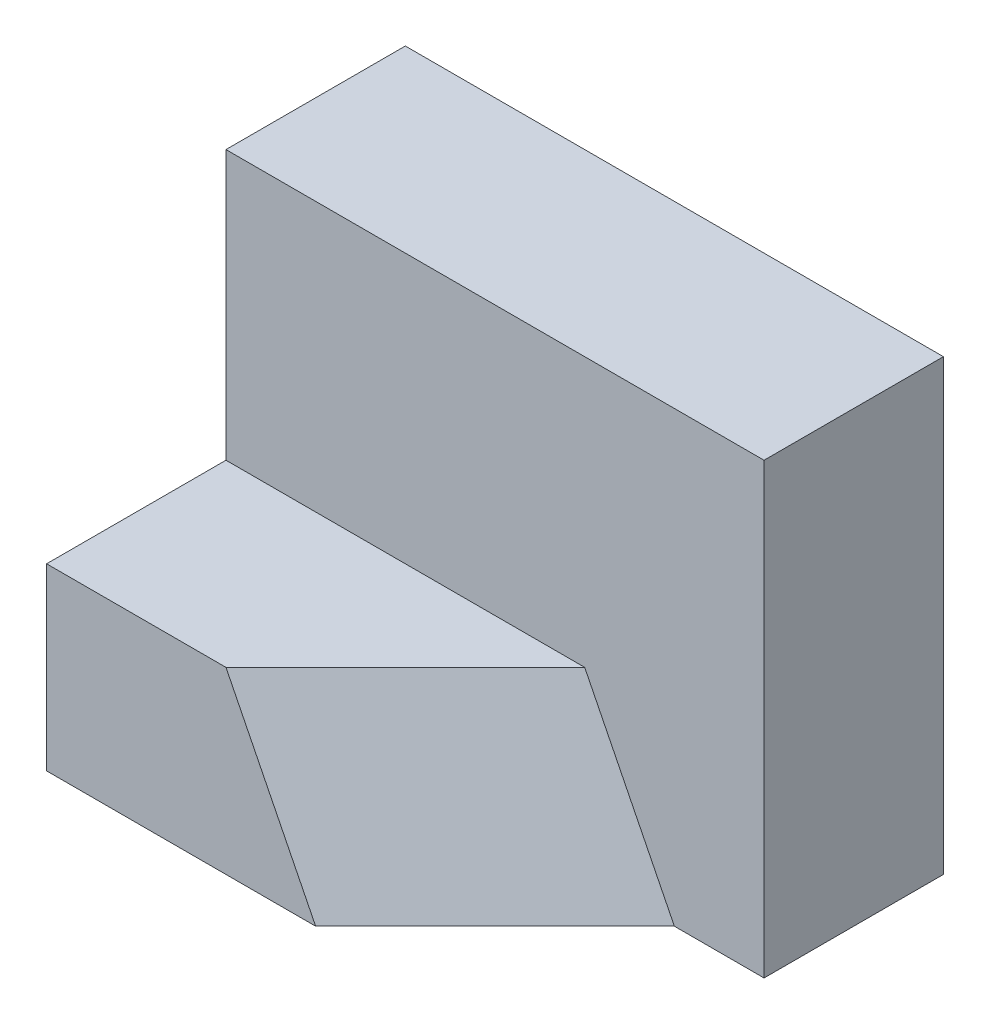
SolidWorks part; units mm, degrees
ref_plane "Front Plane" through (0, 0, 0) normal (0, 0, 1) x (1, 0, 0)
ref_plane "Top Plane" through (0, 0, 0) normal (0, 1, 0) x (1, 0, 0)
ref_plane "Right Plane" through (0, 0, 0) normal (1, 0, 0) x (0, 0, -1)
sketch "Sketch1" plane through (0, 0, 0) normal (0, 0, 1) x (1, 0, 0)
  line L1 (0, 0) -> (6, 0)
  line L2 (0, 0) -> (0, 5)
  line L3 (0, 5) -> (6, 5)
  line L4 (6, 0) -> (6, 5)
  dimension "D1" = 6
  dimension "D2" = 5
extrude "Boss-Extrude1" add sketch "Sketch1" along normal blind 2
sketch "Sketch2" plane through (0, 0, 2) normal (0, 0, 1) x (1, 0, 0)
  line L0 (0, 0) -> (0, 2)
  line L1 (0, 5) -> (0, 0) construction
  line L2 (0, 2) -> (4, 2)
  line L3 (4, 2) -> (6, 0)
  line L4 (0, 0) -> (6, 0) construction
  line L5 (6, 0) -> (0, 0)
  dimension "D1" = 4
  dimension "D2" = 6
  dimension "D3" = 2
extrude "Boss-Extrude2" add sketch "Sketch2" along normal blind 2
sketch3d "3DSketch1"
  line L0 (4, 2, 4) -> (0, 2, 4) construction
  line L1 (0, 0, 4) -> (6, 0, 4) construction
  line L2 (0, 2, 4) -> (0, 0, 4) construction
  line L3 (6, 0, 4) -> (6, 0, 2) construction
  line L4 (5, 0, 2) -> (3, 0, 4)
  line L5 (3, 0, 4) -> (2, 2, 4)
  line L6 (2, 2, 4) -> (4, 2, 2)
  line L7 (4, 2, 2) -> (5, 0, 2)
  point P0 (4, 2, 2)
  point P1 (2, 2, 4)
  point P3 (3, 0, 4)
  point P6 (5, 0, 2)
  dimension "D1" = 2
  dimension "D2" = 3
  dimension "D3" = 2
  dimension "D4" = 1
extrude "Cut-Extrude1" cut sketch "3DSketch1" along direction (-1, 0, 0) on the side of the normal blind 10
